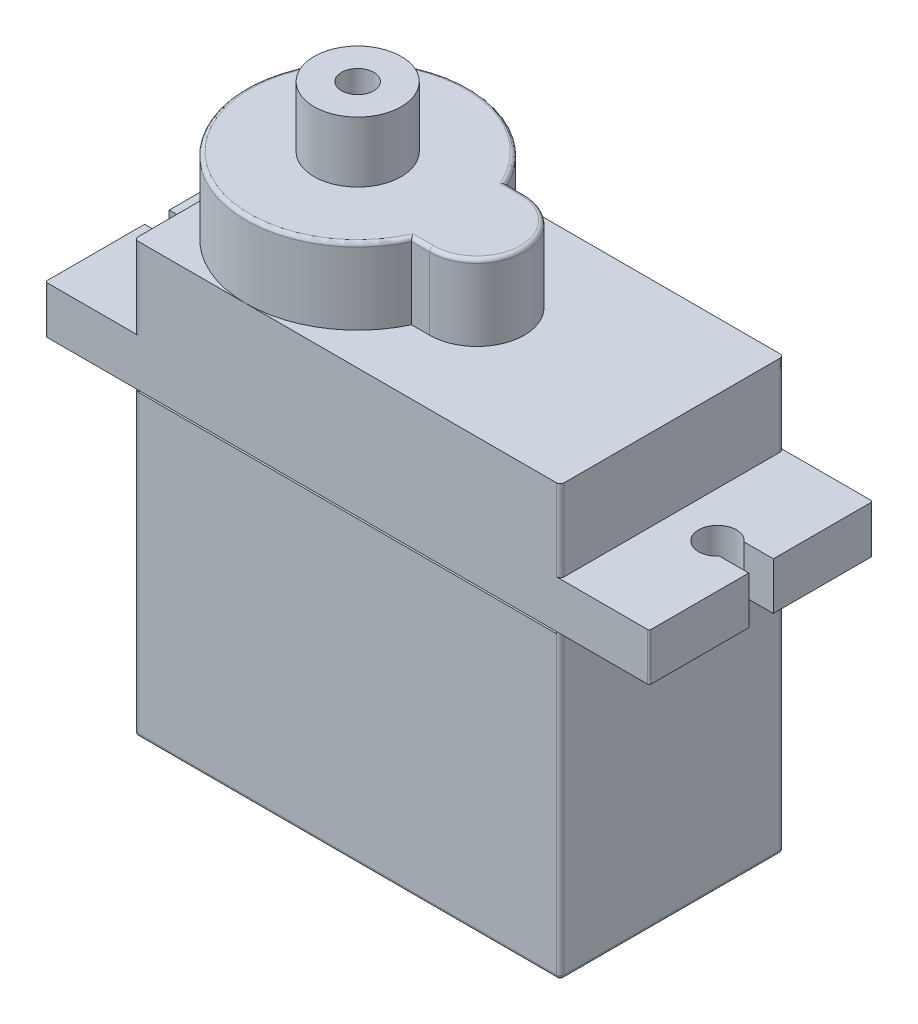
SolidWorks part; units mm, degrees
ref_plane "Front Plane" through (0, 0, 0) normal (0, 0, 1) x (1, 0, 0)
ref_plane "Top Plane" through (0, 0, 0) normal (0, 1, 0) x (1, 0, 0)
ref_plane "Right Plane" through (0, 0, 0) normal (1, 0, 0) x (0, 0, -1)
sketch "Sketch1" plane through (0, 0, 0) normal (0, 0, 1) x (1, 0, 0)
  line L1 (0, 0) -> (22.5, 0)
  line L2 (0, 0) -> (0, 22.7)
  line L3 (0, 22.7) -> (22.5, 22.7)
  line L4 (22.5, 0) -> (22.5, 22.7)
  dimension "D1" = 22.5
  dimension "D2" = 22.7
extrude "Boss-Extrude1" add sketch "Sketch1" along normal blind 11.8
sketch "Sketch2" plane through (22.5, 0, 0) normal (1, 0, 0) x (0, 0, -1)
  line L0 (-11.8, 0) -> (-11.8, 22.7) construction
  line L1 (-11.8, 18.4) -> (0, 18.4)
  line L2 (-11.8, 18.4) -> (-11.8, 15.9)
  line L3 (-11.8, 15.9) -> (0, 15.9)
  line L4 (0, 18.4) -> (0, 15.9)
  line L5 (0, 0) -> (0, 22.7) construction
  line L6 (-11.8, 0) -> (0, 0) construction
  dimension "D1" = 2.5
  dimension "D2" = 15.9
extrude "Boss-Extrude2" add sketch "Sketch2" along normal blind 4.7
sketch "Sketch3" plane through (0, 0, 0) normal (-1, 0, 0) x (0, 0, 1)
  line L0 (0, 22.7) -> (0, 0) construction
  line L1 (0, 18.4) -> (11.8, 18.4)
  line L2 (0, 18.4) -> (0, 15.9)
  line L3 (0, 15.9) -> (11.8, 15.9)
  line L4 (11.8, 18.4) -> (11.8, 15.9)
  line L5 (11.8, 22.7) -> (11.8, 0) construction
  line L6 (11.8, 0) -> (0, 0) construction
  dimension "D1" = 2.5
  dimension "D2" = 15.9
extrude "Boss-Extrude3" add sketch "Sketch3" along normal blind 4.7
sketch "Sketch4" plane through (0, 18.4, 0) normal (0, 1, 0) x (1, 0, 0)
  line L0 (27.2, 0) -> (27.2, -11.8) construction
  line L1 (27.2, -11.8) -> (22.5, -11.8) construction
  line L2 (27.2, -5.25) -> (25.6599, -5.25)
  line L3 (27.2, -6.55) -> (25.6599, -6.55)
  line L4 (27.2, -5.25) -> (27.2, -6.55)
  line L9 (-4.7, -11.8) -> (-4.7, 0) construction
  line L10 (-4.7, -5.25) -> (-3.1599, -5.25)
  line L11 (-3.1599, -6.55) -> (-4.7, -6.55)
  line L12 (-4.7, -5.25) -> (-4.7, -6.55)
  arc A0 (25.6599, -5.25) -> (25.6599, -6.55) centre (24.9, -5.9) ccw
  arc A2 (-3.1599, -6.55) -> (-3.1599, -5.25) centre (-2.4, -5.9) ccw
  point P12 (27.2, -5.9)
  point P14 (-4.7, -5.9)
  point P19 (-3.93, -6.55)
  dimension "D1" = 2
  dimension "D2" = 2.3
  dimension "D6" = 2
  dimension "D7" = 2.3
  dimension "D8" = 0
  dimension "D3" = 5.9
  dimension "D4" = 1.3
  dimension "D5" = 0.65
  dimension "D9" = 1.3
  dimension "D10" = 0.65
extrude "Cut-Extrude1" cut sketch "Sketch4" against normal blind 4.7
sketch "Sketch5" plane through (0, 22.7, 0) normal (0, 1, 0) x (1, 0, 0)
  line L0 (22.5, -11.8) -> (0, -11.8) construction
  line L1 (0, -11.8) -> (0, 0) construction
  line L2 (22.5, 0) -> (0, 0) construction
  line L3 (22.5, -11.8) -> (22.5, 0) construction
  line L4 (12.2, -3.4) -> (11.2442, -3.4)
  line L5 (12.2, -8.4) -> (11.2442, -8.4)
  arc A0 (11.2442, -3.4) -> (11.2442, -8.4) centre (5.9, -5.9) ccw
  arc A1 (12.2, -8.4) -> (12.2, -3.4) centre (12.2, -5.9) ccw
  dimension "D1" = 11.8
  dimension "D2" = 5.9
  dimension "D3" = 5.9
  dimension "D4" = 5
  dimension "D5" = 5.9
  dimension "D6" = 10.3
extrude "Boss-Extrude4" add sketch "Sketch5" along normal blind 4
sketch "Sketch6" plane through (0, 26.7, 0) normal (0, 1, 0) x (1, 0, 0)
  circle A0 centre (5.9, -5.9) radius 2.3
  circle A1 centre (5.9, -5.9) radius 0.85
  dimension "D1" = 4.6
  dimension "D2" = 1.7
extrude "Boss-Extrude5" add sketch "Sketch6" along normal blind 3.2
sketch "Sketch7" plane through (0, 0, 0) normal (0, 0, -1) x (-1, 0, 0)
  text T0 "SG 90"
extrude "Cut-Extrude2" cut sketch "Sketch7" against normal blind 0.1
fillet "Fillet1" radius 0.2 16 edges at (11.7221, 26.7, 8.4) (14.7, 26.7, 5.9) (11.25, 0, 11.8) (0, 7.95, 11.8) (0, 20.55, 11.8) (0, 0, 5.9) (0, 7.95, 0) (0, 20.55, 0) (11.7221, 26.7, 3.4) (0, 26.7, 5.9) (22.5, 20.55, 0) (22.5, 20.55, 11.8) (22.5, 7.95, 11.8) (22.5, 0, 5.9) (11.25, 0, 0) (22.5, 7.95, 0)
sketch "Sketch8" plane through (0, 0, 0) normal (0, 0, -1) x (-1, 0, 0)
  line L1 (-0.2, 15.9) -> (-22.3, 15.9)
  line L2 (-0.2, 15.9) -> (-0.2, 15.8)
  line L3 (-0.2, 15.8) -> (-22.3, 15.8)
  line L4 (-22.3, 15.9) -> (-22.3, 15.8)
  dimension "D1" = 0.1
extrude "Cut-Extrude3" cut sketch "Sketch8" against normal blind 0.1
sketch "Sketch9" plane through (0, 0, 11.8) normal (0, 0, 1) x (1, 0, 0)
  line L0 (22.3, 0.2) -> (22.3, 15.9) construction
  line L1 (0.2, 15.9) -> (22.3, 15.9)
  line L2 (0.2, 15.9) -> (0.2, 15.8)
  line L3 (0.2, 15.8) -> (22.3, 15.8)
  line L4 (22.3, 15.9) -> (22.3, 15.8)
  dimension "D1" = 0.1
extrude "Cut-Extrude4" cut sketch "Sketch9" against normal blind 0.1
fillet "Fillet2" radius 0.1 4 edges at (-4.7, 17.15, 11.8) (-4.7, 17.15, 0) (27.2, 17.15, 0) (27.2, 17.15, 11.8)
ref_plane "Plane1" through (0, 0, 11.8) normal (0, 0, 1) x (1, 0, 0)
sketch "Sketch12" plane through (0, 0, 11.8) normal (0, 0, 1) x (1, 0, 0)
  line L0 (73.8333, 165) -> (369.1667, 165) construction
